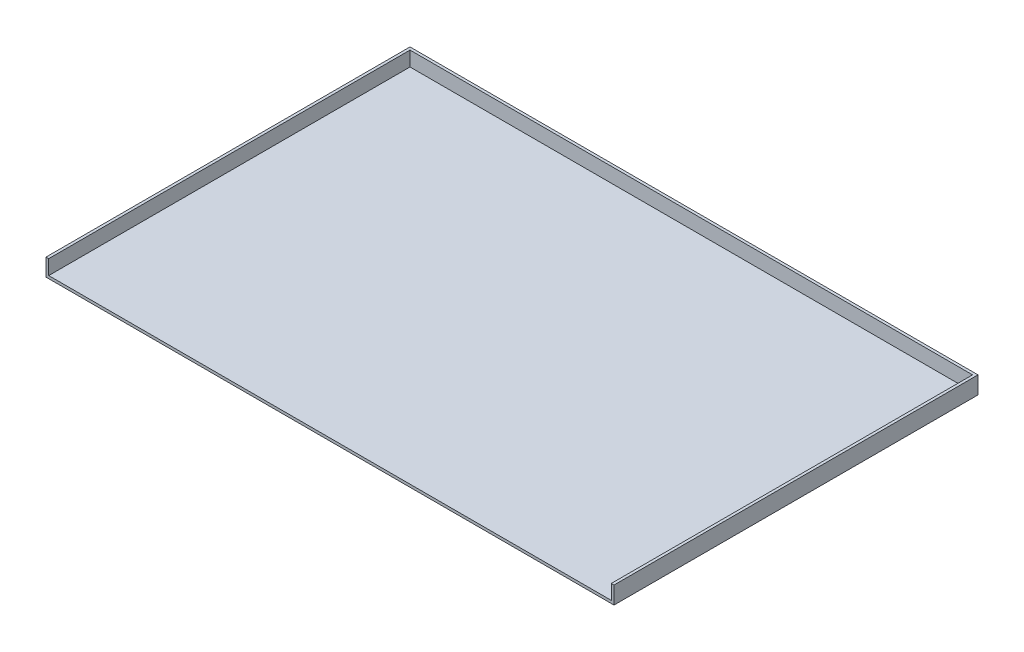
SolidWorks part; units mm, degrees
material "PPS"
ref_plane "Płaszczyzna XY" through (0, 0, 0) normal (0, 0, 1) x (1, 0, 0)
ref_plane "Płaszczyzna XZ" through (0, 0, 0) normal (0, 1, 0) x (1, 0, 0)
ref_plane "Płaszczyzna YZ" through (0, 0, 0) normal (1, 0, 0) x (0, 0, -1)
sketch "Szkic1" plane through (0, 0, 0) normal (0, 0, 1) x (1, 0, 0)
  line L1 (-193.5, -0.925) -> (193.5, -0.925)
  line L2 (-193.5, -0.925) -> (-193.5, 0.925)
  line L3 (-193.5, 0.925) -> (193.5, 0.925)
  line L4 (193.5, -0.925) -> (193.5, 0.925)
  line L5 (-193.5, -0.925) -> (193.5, 0.925) construction
  line L6 (-193.5, 0.925) -> (193.5, -0.925) construction
  point P0 (0, 0)
  dimension "D1" = 387
  dimension "D2" = 1.85
extrude "Dodanie-wyciągnięcie1" add sketch "Szkic1" along normal blind 248
sketch "Szkic3" plane through (0, 0.925, 0) normal (0, 1, 0) x (1, 0, 0)
  line L0 (193.5, -248) -> (193.5, 0)
  line L1 (193.5, -248) -> (-193.5, -248) construction
  line L2 (193.5, 0) -> (-193.5, 0) construction
  line L3 (193.5, -248) -> (193.5, 0) construction
  line L4 (193.5, 0) -> (-193.5, 0)
  line L5 (-193.5, -248) -> (-193.5, 0) construction
  line L6 (-193.5, 0) -> (-193.5, -248)
  line L7 (-193.5, -248) -> (-191.65, -248)
  line L8 (-191.65, -248) -> (-191.65, -1.85)
  line L9 (-191.65, -1.85) -> (191.65, -1.85)
  line L10 (191.65, -1.85) -> (191.65, -248)
  line L11 (191.65, -248) -> (193.5, -248)
  dimension "D1" = 1.85
  dimension "D2" = 1.85
  dimension "D3" = 1.85
extrude "Dodanie-wyciągnięcie2" add sketch "Szkic3" along normal blind 10
